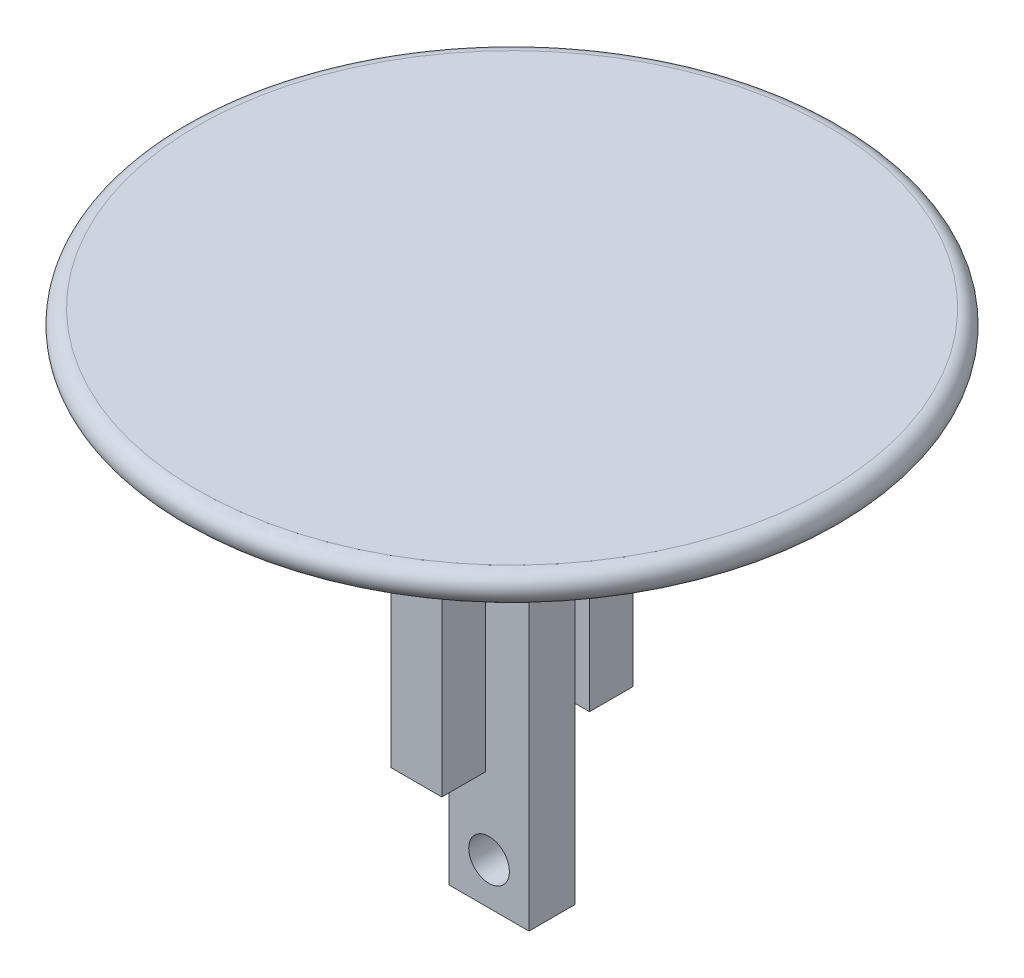
SolidWorks part; units mm, degrees
ref_plane "Front Plane" through (0, 0, 0) normal (0, 0, 1) x (1, 0, 0)
ref_plane "Top Plane" through (0, 0, 0) normal (0, 1, 0) x (1, 0, 0)
ref_plane "Right Plane" through (0, 0, 0) normal (1, 0, 0) x (0, 0, -1)
sketch "Sketch1" plane through (0, 0, 0) normal (0, 0, 1) x (1, 0, 0)
  line L0 (0, 0) -> (25, 0)
  line L1 (25, 0) -> (10, -10)
  line L2 (10, -10) -> (0, -10)
  line L3 (0, 0) -> (0, -10)
  dimension "D1" = 25
  dimension "D2" = 10
  dimension "D3" = 10
revolve "Revolve1" add sketch "Sketch1" angle 360 about L3
sketch "Sketch2" plane through (0, -10, 0) normal (0, -1, 0) x (1, 0, 0)
  line L0 (0, -10) -> (0, 10) construction
  line L1 (-10, 0) -> (10, 0) construction
  line L2 (2.7486, -1.5839) -> (-2.7514, 1.5861) construction
  line L3 (-2.7514, -1.5839) -> (2.7486, -1.5839)
  line L4 (-2.7514, -1.5839) -> (-2.7514, 1.5861)
  line L5 (-2.7514, 1.5861) -> (2.7486, 1.5861)
  line L6 (2.7486, -1.5839) -> (2.7486, 1.5861)
  line L7 (2.7486, 1.5861) -> (-2.7514, -1.5839) construction
  circle A0 centre (0, 0) radius 10 construction
  dimension "D1" = 3.17
  dimension "D2" = 5.5
extrude "Boss-Extrude1" add sketch "Sketch2" along normal blind 25
sketch "Sketch3" plane through (0, 0, -1.5839) normal (0, 0, -1) x (-1, 0, 0)
  circle A0 centre (0, -32.1284) radius 1.4
  point P2 (0, -32.1284)
extrude "Cut-Extrude1" cut sketch "Sketch3" against normal through all
sketch "Sketch6" plane through (0, -10, 0) normal (0, -1, 0) x (1, 0, 0)
  line L0 (0, -10) -> (0, 10) construction
  line L1 (-1.7514, -6.5839) -> (1.7486, -6.5839)
  line L2 (-1.7514, -6.5839) -> (-1.7514, -3.5839)
  line L3 (-1.7514, -3.5839) -> (1.7486, -3.5839)
  line L4 (1.7486, -6.5839) -> (1.7486, -3.5839)
  line L5 (-2.7514, -1.5839) -> (2.7486, -1.5839) construction
  line L6 (2.7486, -1.5839) -> (2.7486, 1.5861) construction
  line L8 (2.7486, 1.5861) -> (-2.7514, 1.5861) construction
  line L9 (-1.7514, 3.5861) -> (1.7486, 3.5861)
  line L10 (-1.7514, 3.5861) -> (-1.7514, 6.5861)
  line L11 (-1.7514, 6.5861) -> (1.7486, 6.5861)
  line L12 (1.7486, 3.5861) -> (1.7486, 6.5861)
  line L13 (2.7486, -1.5839) -> (2.7486, 1.5861) construction
  circle A0 centre (0, 0) radius 10 construction
  dimension "D1" = 2
  dimension "D2" = 1
  dimension "D3" = 3.5
  dimension "D4" = 3
  dimension "D5" = 3
  dimension "D6" = 3.5
  dimension "D7" = 2
  dimension "D8" = 1
extrude "Boss-Extrude2" add sketch "Sketch6" along normal blind 15
fillet "Fillet2" radius 1 1 edges at (-25, 0, 0)
